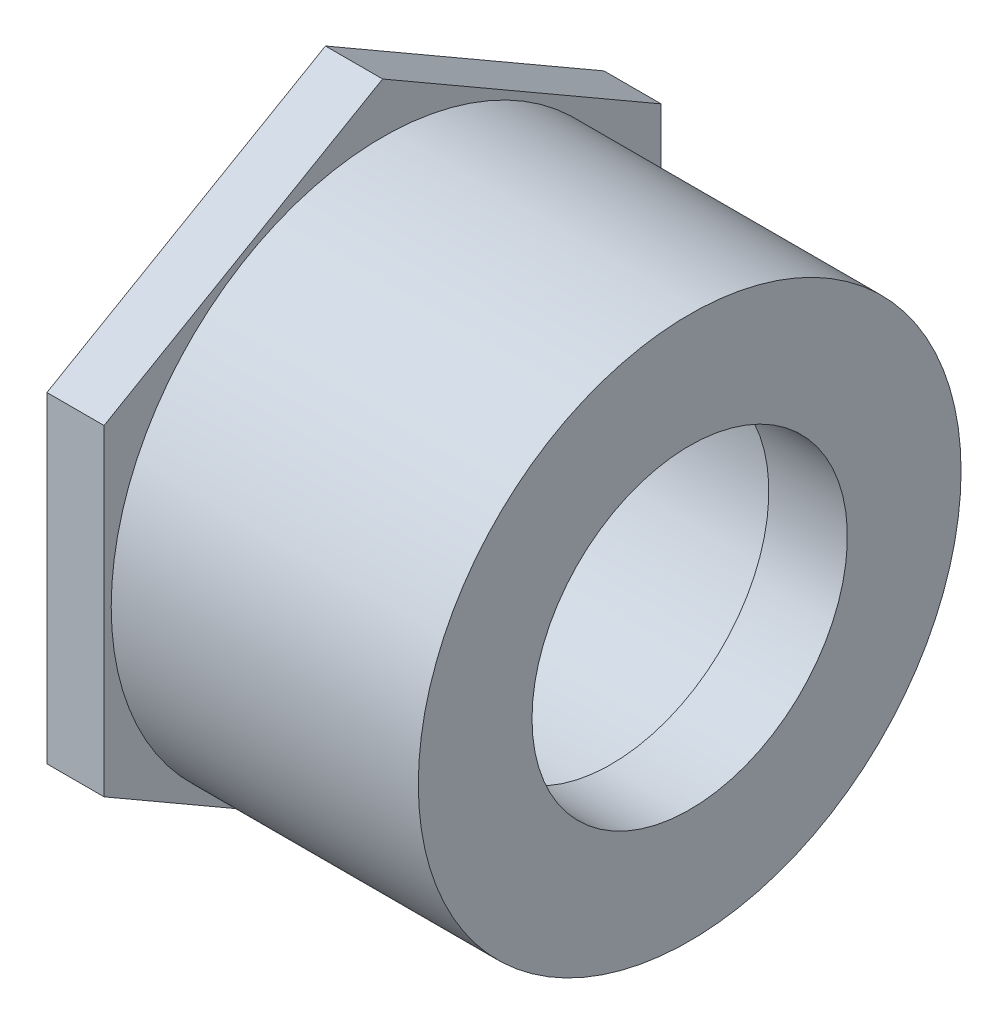
SolidWorks part; units mm, degrees
ref_plane "Front Plane" through (0, 0, 0) normal (0, 0, 1) x (1, 0, 0)
ref_plane "Top Plane" through (0, 0, 0) normal (0, 1, 0) x (1, 0, 0)
ref_plane "Right Plane" through (0, 0, 0) normal (1, 0, 0) x (0, 0, -1)
sketch "Sketch0" plane through (0, 0, 0) normal (0, 0, 1) x (1, 0, 0)
  line L0 (-40.4812, 0) -> (0, 0) construction
  line L2 (-29.3624, 30.1625) -> (-29.3624, -30.1625) construction
  line L3 (-34.1312, 30.9562) -> (-34.1312, -30.9562) construction
  line L5 (-8.7312, 21.0185) -> (-40.4812, 21.209) construction
  line L6 (-8.7312, 21.0185) -> (-8.7312, -21.0185) construction
  line L7 (-8.7312, -21.0185) -> (-40.4812, -21.209) construction
  line L8 (-40.4812, 21.209) -> (-40.4812, -21.209) construction
  line L14 (-8.7312, 17.526) -> (-8.7312, -17.526) construction
  line L21 (-40.4812, 0) -> (-8.7312, 0) construction
  point P12 (-29.3624, 0)
  point P27 (-34.1312, 0)
  dimension "A" = 40.4812
  dimension "OD A 2" = 42.418
  dimension "OD B 2" = 42.037
  dimension "ID 2" = 35.052
  dimension "B" = 8.7312
  dimension "Pipe OD 1" = 60.325
  dimension "C 1" = 29.3624
  dimension "J" = 61.9125
  dimension "K" = 6.35
sketch "Sketch1" plane through (0, 0, 0) normal (0, 0, 1) x (1, 0, 0)
  line L0 (-40.4812, 0) -> (0, 0) construction
  line L1 (-40.4812, 0) -> (0, 0) construction
  line L2 (-40.4812, -30.1625) -> (0, -30.1625)
  line L3 (0, -17.526) -> (0, -30.1625)
  line L4 (-40.4812, -30.1625) -> (-40.4812, -21.209)
  line L5 (-40.4812, -21.209) -> (-8.7312, -21.0185)
  line L6 (0, 0) -> (0, -17.526) construction
  line L8 (-8.7312, -17.526) -> (-8.7312, -21.0185)
  line L11 (-8.7312, -17.526) -> (0, -17.526)
revolve "Revolve1" add sketch "Sketch1" angle 360 about L1
sketch "Sketch2" plane through (-40.4812, 0, 0) normal (-1, 0, 0) x (0, 0, 1)
  line L0 (0, 0) -> (0, 35.7452) construction
  line L1 (0, 35.7452) -> (-30.9563, 17.8726)
  line L2 (-30.9563, 17.8726) -> (-30.9563, -17.8726)
  line L3 (-30.9563, -17.8726) -> (0, -35.7452)
  line L4 (0, -35.7452) -> (30.9563, -17.8726)
  line L5 (30.9563, -17.8726) -> (30.9563, 17.8726)
  line L6 (30.9563, 17.8726) -> (0, 35.7452)
  circle A0 centre (0, 0) radius 21.209 construction
  circle A1 centre (0, 0) radius 21.209
  circle A2 centre (0, 0) radius 30.9562 construction
  point P3 (0, 30.9562)
extrude "Boss-Extrude1" add sketch "Sketch2" against normal up to vertex (6.35 mm away) up to point (-34.1312, 0, 0)
